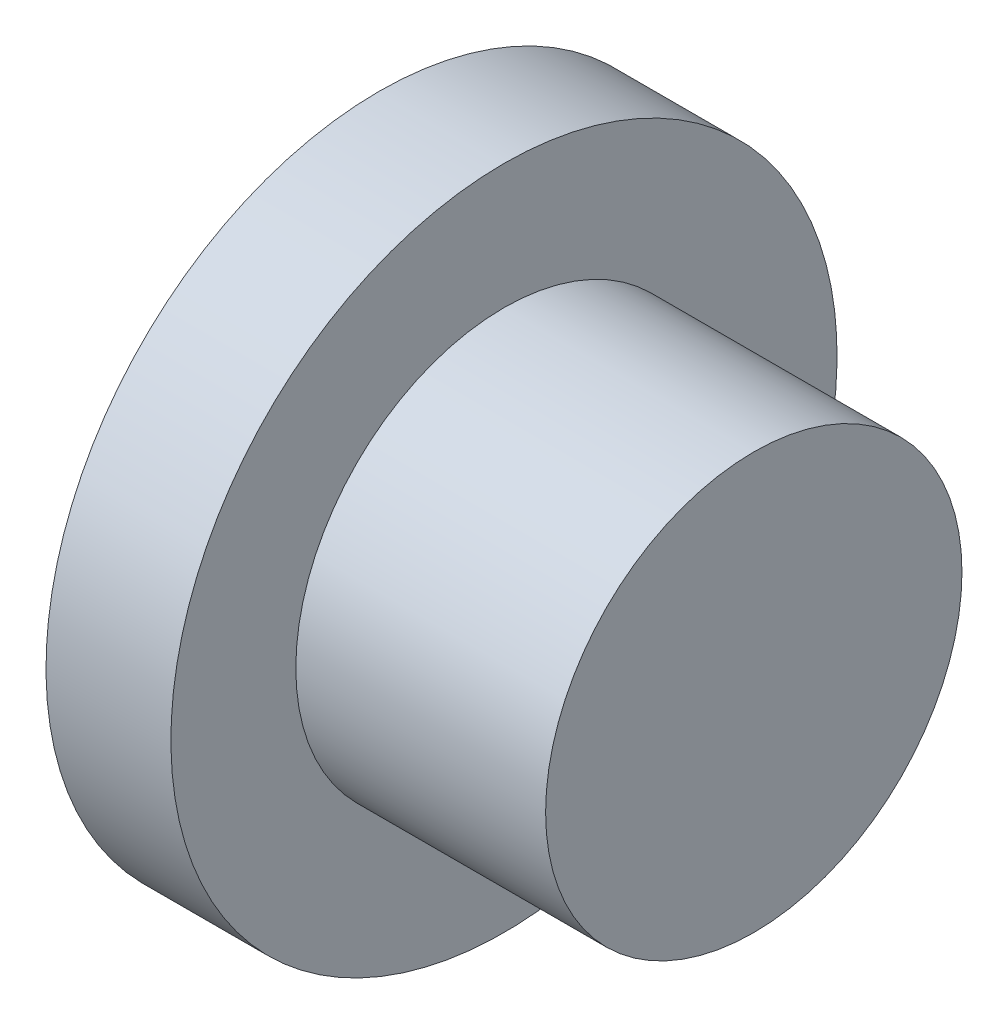
SolidWorks part; units mm, degrees
ref_plane "Face" through (0, 0, 0) normal (0, 0, 1) x (1, 0, 0)
ref_plane "Dessus" through (0, 0, 0) normal (0, 1, 0) x (1, 0, 0)
ref_plane "Droite" through (0, 0, 0) normal (1, 0, 0) x (0, 0, -1)
sketch "Esquisse1" plane through (0, 0, 0) normal (0, 0, 1) x (1, 0, 0)
  line L0 (0, 0) -> (0, 4)
  line L1 (0, 4) -> (1.5, 4)
  line L2 (1.5, 4) -> (1.5, 2.5)
  line L3 (1.5, 2.5) -> (4.5, 2.5)
  line L4 (4.5, 2.5) -> (4.5, 0)
  line L5 (4.5, 0) -> (0, 0)
  dimension "D1" = 4
  dimension "D2" = 1.5
  dimension "D3" = 4.5
  dimension "D4" = 2.5
revolve "Révolution1" add sketch "Esquisse1" angle 360 about L5
